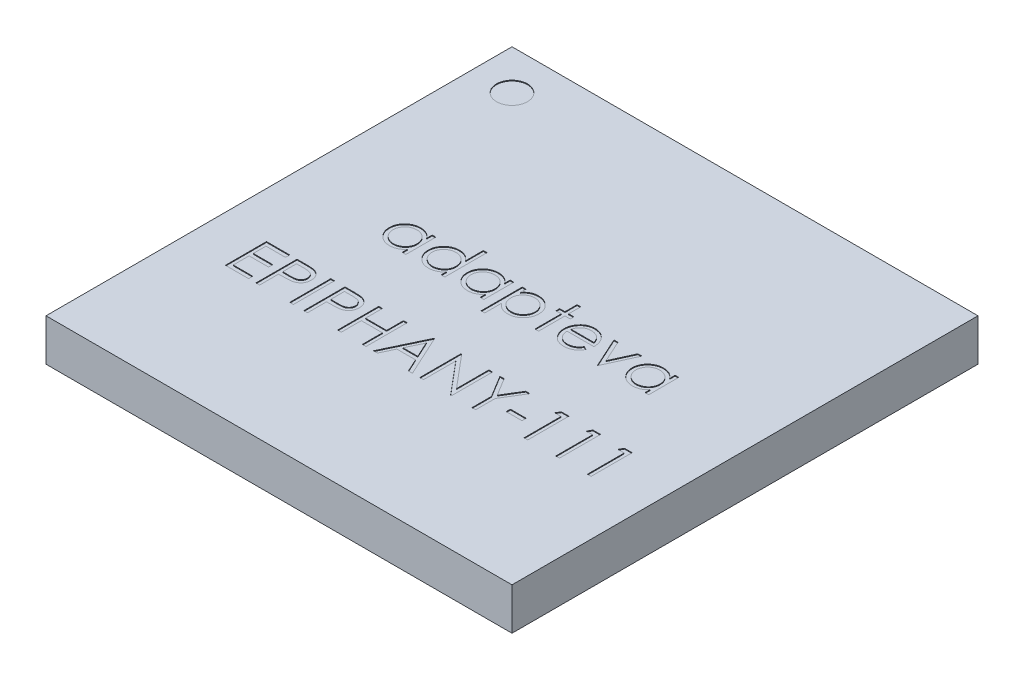
SolidWorks part; units mm, degrees
ref_plane "Front Plane" through (0, 0, 0) normal (0, 0, 1) x (1, 0, 0)
ref_plane "Top Plane" through (0, 0, 0) normal (0, 1, 0) x (1, 0, 0)
ref_plane "Right Plane" through (0, 0, 0) normal (1, 0, 0) x (0, 0, -1)
sketch "Sketch1" plane through (0, 0, 0) normal (0, 1, 0) x (1, 0, 0)
  line L1 (0, 0) -> (15.0002, 0)
  line L2 (0, 0) -> (0, 15.0002)
  line L3 (0, 15.0002) -> (15.0002, 15.0002)
  line L4 (15.0002, 0) -> (15.0002, 15.0002)
  dimension "D2" = 15.0002
extrude "Boss-Extrude1" add sketch "Sketch1" along normal blind 1.35
sketch "Sketch2" plane through (0, 1.35, 0) normal (0, 1, 0) x (1, 0, 0)
  line L0 (7.5001, 15.0002) -> (7.5001, 0) construction
  line L1 (15.0002, 15.0002) -> (0, 15.0002) construction
  line L2 (0, 0) -> (15.0002, 0) construction
  line L3 (0, 7.5001) -> (15.0002, 7.5001) construction
  line L4 (0, 15.0002) -> (0, 0) construction
  line L5 (15.0002, 0) -> (15.0002, 15.0002) construction
  line L6 (1.2833, 15.0002) -> (1.2833, 13.7169) construction
  line L7 (1.2833, 13.7169) -> (0, 13.7169) construction
  circle A0 centre (1.2833, 13.7169) radius 0.4984
  text T0 "adapteva\r\nEPIPHANY-111" font "Century Gothic" height in points 5
extrude "Cut-Extrude1" cut sketch "Sketch2" against normal blind 0.0254
